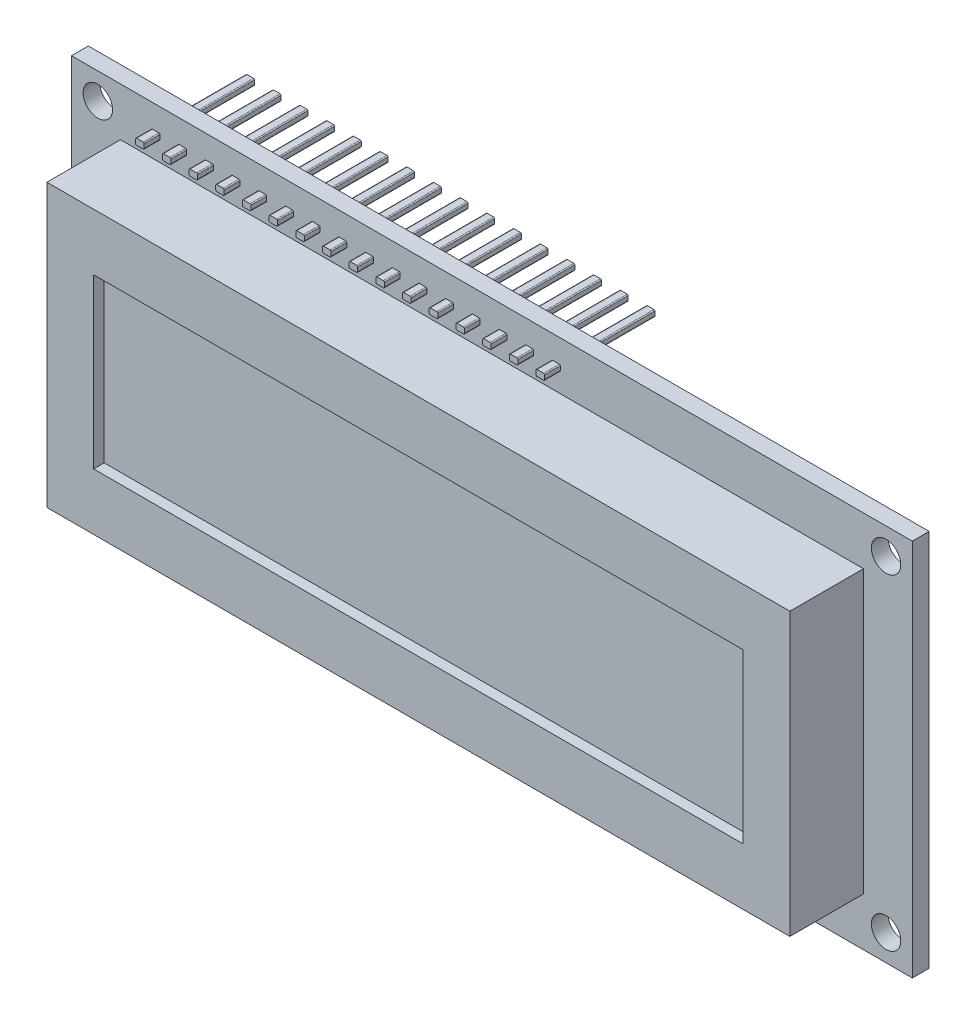
SolidWorks part; units mm, degrees
ref_plane "Plan de face" through (0, 0, 0) normal (0, 0, 1) x (1, 0, 0)
ref_plane "Plan de dessus" through (0, 0, 0) normal (0, 1, 0) x (1, 0, 0)
ref_plane "Plan de droite" through (0, 0, 0) normal (1, 0, 0) x (0, 0, -1)
sketch "Esquisse1" plane through (0, 0, 0) normal (0, 0, 1) x (1, 0, 0)
  line L0 (40, 36) -> (40, 0) construction
  line L1 (0, 0) -> (80, 0)
  line L2 (0, 0) -> (0, 36)
  line L3 (0, 36) -> (80, 36)
  line L4 (80, 0) -> (80, 36)
  line L5 (0, 18) -> (80, 18) construction
  circle A0 centre (2.5, 33.5) radius 1.4
  circle A1 centre (77.5, 33.5) radius 1.4
  circle A2 centre (77.5, 2.5) radius 1.4
  circle A3 centre (2.5, 2.5) radius 1.4
  dimension "D3" = 2.8
  dimension "D1" = 80
  dimension "D2" = 36
  dimension "D4" = 2.5
  dimension "D5" = 2.5
extrude "Boss.-Extru.1" add sketch "Esquisse1" along normal blind 1.6
sketch "Esquisse2" plane through (0, 0, 1.6) normal (0, 0, 1) x (1, 0, 0)
  line L0 (0, 18) -> (80, 18) construction
  line L1 (4.65, 31.4) -> (75.35, 31.4)
  line L2 (4.65, 31.4) -> (4.65, 4.6)
  line L3 (4.65, 4.6) -> (75.35, 4.6)
  line L4 (75.35, 31.4) -> (75.35, 4.6)
  line L5 (0, 36) -> (0, 0) construction
  line L6 (80, 0) -> (80, 36) construction
  line L7 (40, 36) -> (40, 0) construction
  line L8 (80, 36) -> (0, 36) construction
  line L9 (0, 0) -> (80, 0) construction
  dimension "D1" = 70.7
  dimension "D2" = 26.8
  dimension "D3" = 13.4
  dimension "D4" = 35.35
extrude "Boss.-Extru.2" add sketch "Esquisse2" along normal blind 7
sketch "Esquisse3" plane through (0, 0, 8.6) normal (0, 0, 1) x (1, 0, 0)
  line L1 (9.1, 26) -> (70.9, 26)
  line L2 (9.1, 26) -> (9.1, 10)
  line L3 (9.1, 10) -> (70.9, 10)
  line L4 (70.9, 26) -> (70.9, 10)
  line L5 (40, 31.4) -> (40, 4.6) construction
  line L6 (75.35, 31.4) -> (4.65, 31.4) construction
  line L7 (4.65, 4.6) -> (75.35, 4.6) construction
  line L8 (75.35, 18) -> (4.65, 18) construction
  line L9 (75.35, 4.6) -> (75.35, 31.4) construction
  line L10 (4.65, 31.4) -> (4.65, 4.6) construction
  dimension "D1" = 61.8
  dimension "D2" = 16
  dimension "D3" = 8
  dimension "D4" = 30.9
extrude "Enlèv. mat.-Extru.1" cut sketch "Esquisse3" against normal blind 1
sketch "Esquisse4" plane through (0, 0, 1.6) normal (0, 0, 1) x (1, 0, 0)
  line L0 (2.5, 33.5) -> (8.5, 33.5) construction
  line L2 (7.6948, 33.7929) -> (8.3052, 33.7929)
  line L3 (8.4052, 33.6929) -> (8.4052, 33.3071)
  line L4 (8.3052, 33.2071) -> (7.6948, 33.2071)
  line L5 (7.5948, 33.3071) -> (7.5948, 33.6929)
  line L6 (10.2348, 33.7929) -> (10.8452, 33.7929)
  line L7 (10.1348, 33.3071) -> (10.1348, 33.6929)
  line L8 (10.8452, 33.2071) -> (10.2348, 33.2071)
  line L9 (10.9452, 33.6929) -> (10.9452, 33.3071)
  line L10 (12.7748, 33.7929) -> (13.3852, 33.7929)
  line L11 (12.6748, 33.3071) -> (12.6748, 33.6929)
  line L12 (13.3852, 33.2071) -> (12.7748, 33.2071)
  line L13 (13.4852, 33.6929) -> (13.4852, 33.3071)
  line L14 (15.3148, 33.7929) -> (15.9252, 33.7929)
  line L15 (15.2148, 33.3071) -> (15.2148, 33.6929)
  line L16 (15.9252, 33.2071) -> (15.3148, 33.2071)
  line L17 (16.0252, 33.6929) -> (16.0252, 33.3071)
  line L18 (17.8548, 33.7929) -> (18.4652, 33.7929)
  line L19 (17.7548, 33.3071) -> (17.7548, 33.6929)
  line L20 (18.4652, 33.2071) -> (17.8548, 33.2071)
  line L21 (18.5652, 33.6929) -> (18.5652, 33.3071)
  line L22 (20.3948, 33.7929) -> (21.0052, 33.7929)
  line L23 (20.2948, 33.3071) -> (20.2948, 33.6929)
  line L24 (21.0052, 33.2071) -> (20.3948, 33.2071)
  line L25 (21.1052, 33.6929) -> (21.1052, 33.3071)
  line L26 (22.9348, 33.7929) -> (23.5452, 33.7929)
  line L27 (22.8348, 33.3071) -> (22.8348, 33.6929)
  line L28 (23.5452, 33.2071) -> (22.9348, 33.2071)
  line L29 (23.6452, 33.6929) -> (23.6452, 33.3071)
  line L30 (25.4748, 33.7929) -> (26.0852, 33.7929)
  line L31 (25.3748, 33.3071) -> (25.3748, 33.6929)
  line L32 (26.0852, 33.2071) -> (25.4748, 33.2071)
  line L33 (26.1852, 33.6929) -> (26.1852, 33.3071)
  line L34 (28.0148, 33.7929) -> (28.6252, 33.7929)
  line L35 (27.9148, 33.3071) -> (27.9148, 33.6929)
  line L36 (28.6252, 33.2071) -> (28.0148, 33.2071)
  line L37 (28.7252, 33.6929) -> (28.7252, 33.3071)
  line L38 (30.5548, 33.7929) -> (31.1652, 33.7929)
  line L39 (30.4548, 33.3071) -> (30.4548, 33.6929)
  line L40 (31.1652, 33.2071) -> (30.5548, 33.2071)
  line L41 (31.2652, 33.6929) -> (31.2652, 33.3071)
  line L42 (33.0948, 33.7929) -> (33.7052, 33.7929)
  line L43 (32.9948, 33.3071) -> (32.9948, 33.6929)
  line L44 (33.7052, 33.2071) -> (33.0948, 33.2071)
  line L45 (33.8052, 33.6929) -> (33.8052, 33.3071)
  line L46 (35.6348, 33.7929) -> (36.2452, 33.7929)
  line L47 (35.5348, 33.3071) -> (35.5348, 33.6929)
  line L48 (36.2452, 33.2071) -> (35.6348, 33.2071)
  line L49 (36.3452, 33.6929) -> (36.3452, 33.3071)
  line L50 (38.1748, 33.7929) -> (38.7852, 33.7929)
  line L51 (38.0748, 33.3071) -> (38.0748, 33.6929)
  line L52 (38.7852, 33.2071) -> (38.1748, 33.2071)
  line L53 (38.8852, 33.6929) -> (38.8852, 33.3071)
  line L54 (40.7148, 33.7929) -> (41.3252, 33.7929)
  line L55 (40.6148, 33.3071) -> (40.6148, 33.6929)
  line L56 (41.3252, 33.2071) -> (40.7148, 33.2071)
  line L57 (41.4252, 33.6929) -> (41.4252, 33.3071)
  line L58 (43.2548, 33.7929) -> (43.8652, 33.7929)
  line L59 (43.1548, 33.3071) -> (43.1548, 33.6929)
  line L60 (43.8652, 33.2071) -> (43.2548, 33.2071)
  line L61 (43.9652, 33.6929) -> (43.9652, 33.3071)
  line L62 (45.7948, 33.7929) -> (46.4052, 33.7929)
  line L63 (45.6948, 33.3071) -> (45.6948, 33.6929)
  line L64 (46.4052, 33.2071) -> (45.7948, 33.2071)
  line L65 (46.5052, 33.6929) -> (46.5052, 33.3071)
  arc A0 (7.6948, 33.2071) -> (7.5948, 33.3071) centre (7.6948, 33.3071) cw
  arc A1 (10.2348, 33.7929) -> (10.1348, 33.6929) centre (10.2348, 33.6929) ccw
  arc A2 (10.2348, 33.2071) -> (10.1348, 33.3071) centre (10.2348, 33.3071) cw
  arc A3 (10.9452, 33.3071) -> (10.8452, 33.2071) centre (10.8452, 33.3071) cw
  arc A4 (10.8452, 33.7929) -> (10.9452, 33.6929) centre (10.8452, 33.6929) cw
  arc A5 (12.7748, 33.7929) -> (12.6748, 33.6929) centre (12.7748, 33.6929) ccw
  arc A6 (12.7748, 33.2071) -> (12.6748, 33.3071) centre (12.7748, 33.3071) cw
  arc A7 (13.4852, 33.3071) -> (13.3852, 33.2071) centre (13.3852, 33.3071) cw
  arc A8 (13.3852, 33.7929) -> (13.4852, 33.6929) centre (13.3852, 33.6929) cw
  arc A9 (15.3148, 33.7929) -> (15.2148, 33.6929) centre (15.3148, 33.6929) ccw
  arc A10 (15.3148, 33.2071) -> (15.2148, 33.3071) centre (15.3148, 33.3071) cw
  arc A11 (16.0252, 33.3071) -> (15.9252, 33.2071) centre (15.9252, 33.3071) cw
  arc A12 (15.9252, 33.7929) -> (16.0252, 33.6929) centre (15.9252, 33.6929) cw
  arc A13 (17.8548, 33.7929) -> (17.7548, 33.6929) centre (17.8548, 33.6929) ccw
  arc A14 (17.8548, 33.2071) -> (17.7548, 33.3071) centre (17.8548, 33.3071) cw
  arc A15 (18.5652, 33.3071) -> (18.4652, 33.2071) centre (18.4652, 33.3071) cw
  arc A16 (18.4652, 33.7929) -> (18.5652, 33.6929) centre (18.4652, 33.6929) cw
  arc A17 (8.4052, 33.3071) -> (8.3052, 33.2071) centre (8.3052, 33.3071) cw
  arc A18 (8.3052, 33.7929) -> (8.4052, 33.6929) centre (8.3052, 33.6929) cw
  arc A19 (7.6948, 33.7929) -> (7.5948, 33.6929) centre (7.6948, 33.6929) ccw
  arc A20 (20.3948, 33.7929) -> (20.2948, 33.6929) centre (20.3948, 33.6929) ccw
  arc A21 (20.3948, 33.2071) -> (20.2948, 33.3071) centre (20.3948, 33.3071) cw
  arc A22 (21.1052, 33.3071) -> (21.0052, 33.2071) centre (21.0052, 33.3071) cw
  arc A23 (21.0052, 33.7929) -> (21.1052, 33.6929) centre (21.0052, 33.6929) cw
  arc A24 (22.9348, 33.7929) -> (22.8348, 33.6929) centre (22.9348, 33.6929) ccw
  arc A25 (22.9348, 33.2071) -> (22.8348, 33.3071) centre (22.9348, 33.3071) cw
  arc A26 (23.6452, 33.3071) -> (23.5452, 33.2071) centre (23.5452, 33.3071) cw
  arc A27 (23.5452, 33.7929) -> (23.6452, 33.6929) centre (23.5452, 33.6929) cw
  arc A28 (25.4748, 33.7929) -> (25.3748, 33.6929) centre (25.4748, 33.6929) ccw
  arc A29 (25.4748, 33.2071) -> (25.3748, 33.3071) centre (25.4748, 33.3071) cw
  arc A30 (26.1852, 33.3071) -> (26.0852, 33.2071) centre (26.0852, 33.3071) cw
  arc A31 (26.0852, 33.7929) -> (26.1852, 33.6929) centre (26.0852, 33.6929) cw
  arc A32 (28.0148, 33.7929) -> (27.9148, 33.6929) centre (28.0148, 33.6929) ccw
  arc A33 (28.0148, 33.2071) -> (27.9148, 33.3071) centre (28.0148, 33.3071) cw
  arc A34 (28.7252, 33.3071) -> (28.6252, 33.2071) centre (28.6252, 33.3071) cw
  arc A35 (28.6252, 33.7929) -> (28.7252, 33.6929) centre (28.6252, 33.6929) cw
  arc A36 (30.5548, 33.7929) -> (30.4548, 33.6929) centre (30.5548, 33.6929) ccw
  arc A37 (30.5548, 33.2071) -> (30.4548, 33.3071) centre (30.5548, 33.3071) cw
  arc A38 (31.2652, 33.3071) -> (31.1652, 33.2071) centre (31.1652, 33.3071) cw
  arc A39 (31.1652, 33.7929) -> (31.2652, 33.6929) centre (31.1652, 33.6929) cw
  arc A40 (33.0948, 33.7929) -> (32.9948, 33.6929) centre (33.0948, 33.6929) ccw
  arc A41 (33.0948, 33.2071) -> (32.9948, 33.3071) centre (33.0948, 33.3071) cw
  arc A42 (33.8052, 33.3071) -> (33.7052, 33.2071) centre (33.7052, 33.3071) cw
  arc A43 (33.7052, 33.7929) -> (33.8052, 33.6929) centre (33.7052, 33.6929) cw
  arc A44 (35.6348, 33.7929) -> (35.5348, 33.6929) centre (35.6348, 33.6929) ccw
  arc A45 (35.6348, 33.2071) -> (35.5348, 33.3071) centre (35.6348, 33.3071) cw
  arc A46 (36.3452, 33.3071) -> (36.2452, 33.2071) centre (36.2452, 33.3071) cw
  arc A47 (36.2452, 33.7929) -> (36.3452, 33.6929) centre (36.2452, 33.6929) cw
  arc A48 (38.1748, 33.7929) -> (38.0748, 33.6929) centre (38.1748, 33.6929) ccw
  arc A49 (38.1748, 33.2071) -> (38.0748, 33.3071) centre (38.1748, 33.3071) cw
  arc A50 (38.8852, 33.3071) -> (38.7852, 33.2071) centre (38.7852, 33.3071) cw
  arc A51 (38.7852, 33.7929) -> (38.8852, 33.6929) centre (38.7852, 33.6929) cw
  arc A52 (40.7148, 33.7929) -> (40.6148, 33.6929) centre (40.7148, 33.6929) ccw
  arc A53 (40.7148, 33.2071) -> (40.6148, 33.3071) centre (40.7148, 33.3071) cw
  arc A54 (41.4252, 33.3071) -> (41.3252, 33.2071) centre (41.3252, 33.3071) cw
  arc A55 (41.3252, 33.7929) -> (41.4252, 33.6929) centre (41.3252, 33.6929) cw
  arc A56 (43.2548, 33.7929) -> (43.1548, 33.6929) centre (43.2548, 33.6929) ccw
  arc A57 (43.2548, 33.2071) -> (43.1548, 33.3071) centre (43.2548, 33.3071) cw
  arc A58 (43.9652, 33.3071) -> (43.8652, 33.2071) centre (43.8652, 33.3071) cw
  arc A59 (43.8652, 33.7929) -> (43.9652, 33.6929) centre (43.8652, 33.6929) cw
  arc A60 (45.7948, 33.7929) -> (45.6948, 33.6929) centre (45.7948, 33.6929) ccw
  arc A61 (45.7948, 33.2071) -> (45.6948, 33.3071) centre (45.7948, 33.3071) cw
  arc A62 (46.5052, 33.3071) -> (46.4052, 33.2071) centre (46.4052, 33.3071) cw
  arc A63 (46.4052, 33.7929) -> (46.5052, 33.6929) centre (46.4052, 33.6929) cw
  dimension "D1" = 0.1
  dimension "D2" = 16
extrude "Boss.-Extru.3" add sketch "Esquisse4" along normal blind 1.5 and the other way blind 9
equation "\"D3@Esquisse2\"=\"D2@Esquisse2\"/2"
equation "\"D4@Esquisse2\"=\"D1@Esquisse2\"/2"
equation "\"D3@Esquisse3\"=\"D2@Esquisse3\"/2"
equation "\"D4@Esquisse3\"=\"D1@Esquisse3\"/2"
